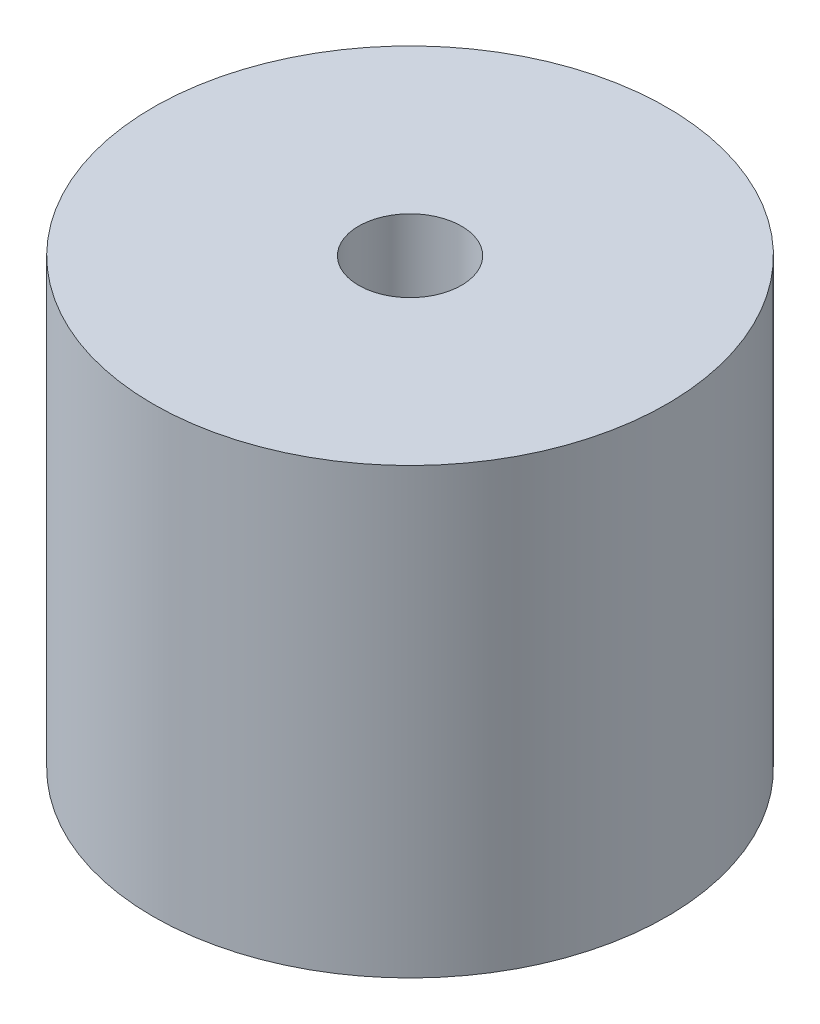
SolidWorks part; units mm, degrees
ref_plane "Front Plane" through (0, 0, 0) normal (0, 0, 1) x (1, 0, 0)
ref_plane "Top Plane" through (0, 0, 0) normal (0, 1, 0) x (1, 0, 0)
ref_plane "Right Plane" through (0, 0, 0) normal (1, 0, 0) x (0, 0, -1)
sketch "Sketch1" plane through (0, 0, 0) normal (0, 1, 0) x (1, 0, 0)
  circle A0 centre (0, 0) radius 10
  circle A1 centre (0, 0) radius 50
  dimension "D1" = 20
  dimension "D2" = 100
extrude "Boss-Extrude1" add sketch "Sketch1" along normal blind 86.36
